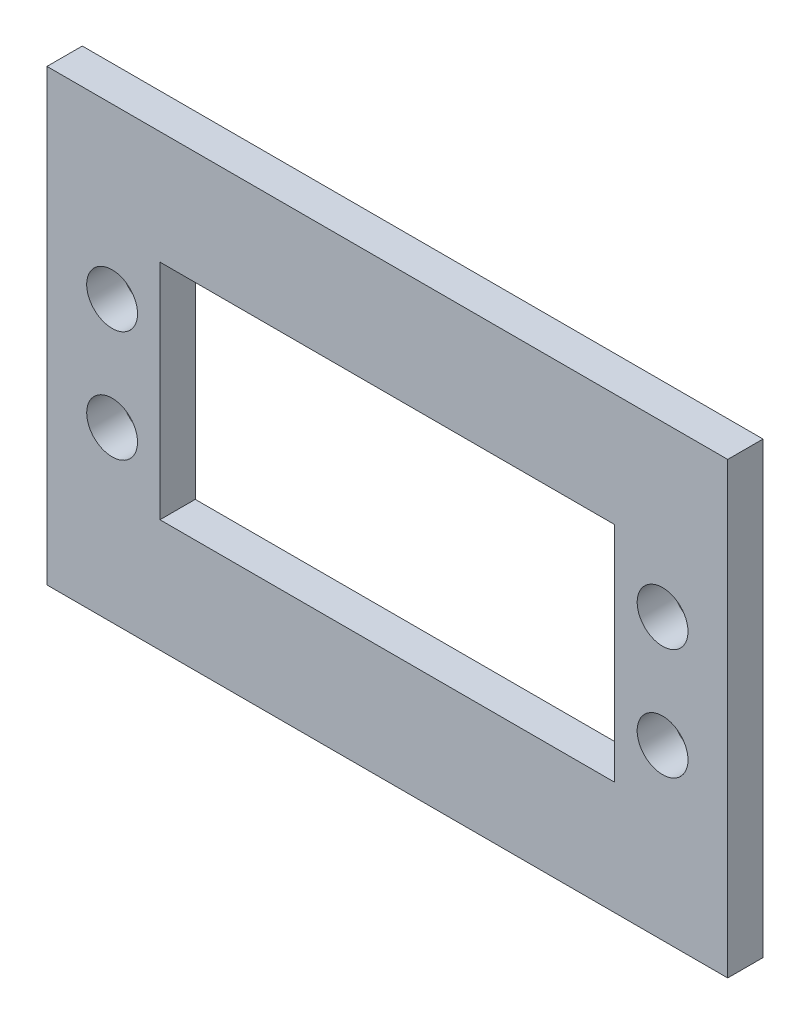
SolidWorks part; units mm, degrees
ref_plane "Front" through (0, 0, 0) normal (0, 0, 1) x (1, 0, 0)
ref_plane "Top" through (0, 0, 0) normal (0, 1, 0) x (1, 0, 0)
ref_plane "Right" through (0, 0, 0) normal (1, 0, 0) x (0, 0, -1)
sketch "Sketch1" plane through (0, 0, 0) normal (0, 0, 1) x (1, 0, 0)
  line L0 (-10.16, -10.16) -> (-10.16, 30.226)
  line L1 (0, 0) -> (40.894, 0)
  line L2 (0, 0) -> (0, 20.066)
  line L3 (0, 20.066) -> (40.894, 20.066)
  line L4 (40.894, 0) -> (40.894, 20.066)
  line L5 (-10.16, 30.226) -> (51.054, 30.226)
  line L6 (51.054, -10.16) -> (51.054, 30.226)
  line L7 (-10.16, -10.16) -> (51.054, -10.16)
  dimension "D1" = 40.894
  dimension "D2" = 20.066
  dimension "D3" = 10.16
extrude "Boss-Extrude1" add sketch "Sketch1" along normal blind 3.175
sketch "Sketch2" plane through (0, 0, 3.175) normal (0, 0, 1) x (1, 0, 0)
  line L0 (20.447, 30.226) -> (20.447, -10.16) construction
  line L1 (51.054, 30.226) -> (-10.16, 30.226) construction
  line L2 (-10.16, -10.16) -> (51.054, -10.16) construction
  line L3 (-10.16, 10.033) -> (51.054, 10.033) construction
  line L4 (-10.16, 30.226) -> (-10.16, -10.16) construction
  line L5 (51.054, -10.16) -> (51.054, 30.226) construction
  circle A0 centre (-4.303, 15.033) radius 2.286
  circle A1 centre (-4.303, 5.033) radius 2.286
  circle A2 centre (45.197, 5.033) radius 2.286
  circle A3 centre (45.197, 15.033) radius 2.286
  dimension "D1" = 4.572
  dimension "D2" = 49.5
  dimension "D3" = 5
extrude "Cut-Extrude1" cut sketch "Sketch2" against normal through all
